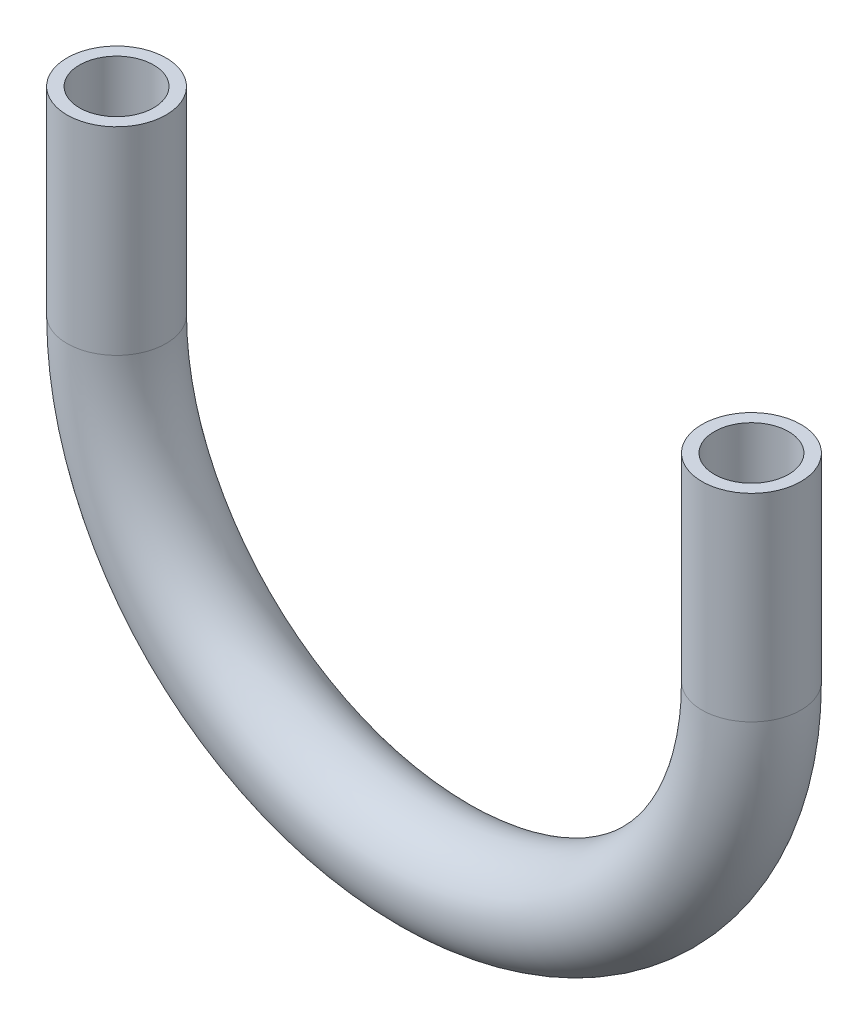
SolidWorks part; units mm, degrees
ref_plane "Front" through (0, 0, 0) normal (0, 0, 1) x (1, 0, 0)
ref_plane "Top" through (0, 0, 0) normal (0, 1, 0) x (1, 0, 0)
ref_plane "Right" through (0, 0, 0) normal (1, 0, 0) x (0, 0, -1)
sketch "Sketch1" plane through (0, 0, 0) normal (0, 0, 1) x (1, 0, 0)
  line L2 (0, 0) -> (0, -50.8)
  line L4 (162.921, 0) -> (162.921, -50.8)
  arc A0 (0, -50.8) -> (162.921, -50.8) centre (81.4605, -50.8) ccw
  dimension "D1" = 162.921
  dimension "D2" = 50.8
  dimension "D3" = 50.8
sketch "Sketch2" plane through (0, 0, 0) normal (0, 1, 0) x (1, 0, 0)
  circle A0 centre (0, 0) radius 9.525
  dimension "D1" = 19.05
sweep "Sweep-Thin1" add profiles "Sketch2" path "Sketch1" parameters "D1"=3.175
